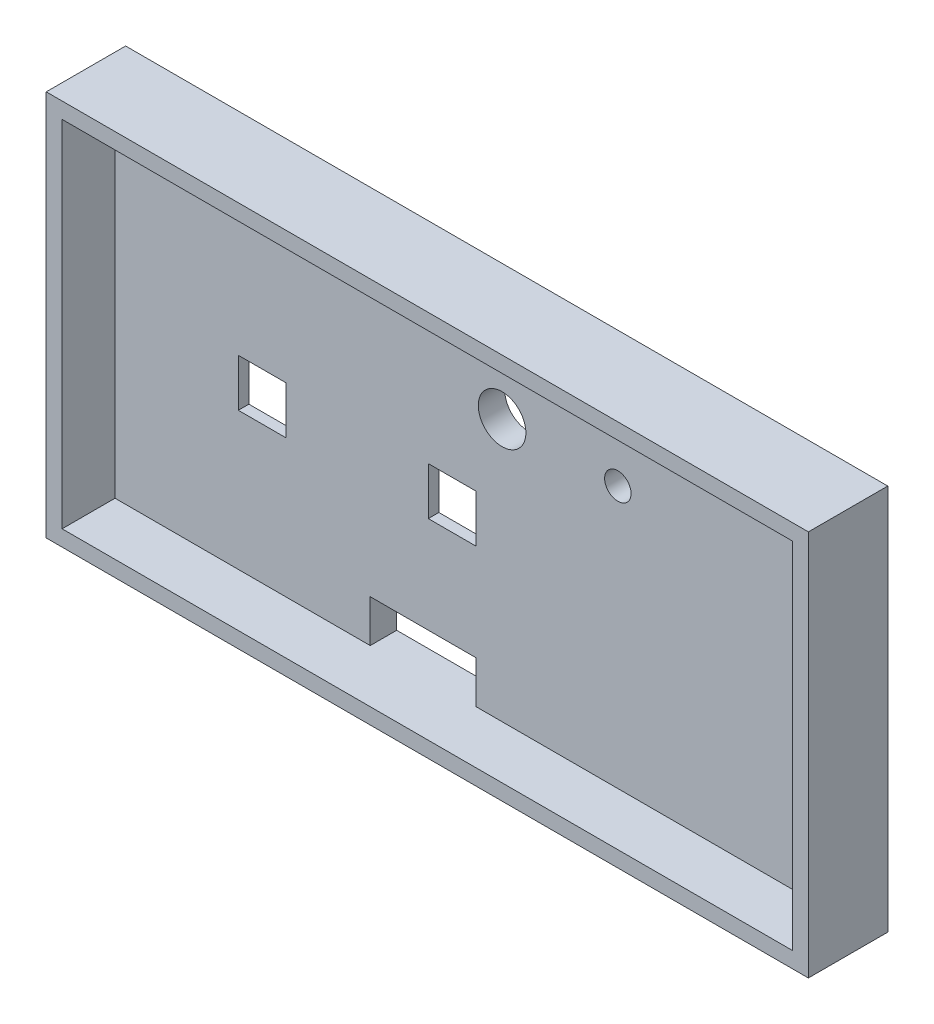
SolidWorks part; units mm, degrees
ref_plane "Plan de face" through (0, 0, 0) normal (0, 0, 1) x (1, 0, 0)
ref_plane "Plan de dessus" through (0, 0, 0) normal (0, 1, 0) x (1, 0, 0)
ref_plane "Plan de droite" through (0, 0, 0) normal (1, 0, 0) x (0, 0, -1)
sketch "Esquisse1" plane through (0, 0, 0) normal (0, 0, 1) x (1, 0, 0)
  line L1 (0, 0) -> (137, 0)
  line L2 (0, 0) -> (0, 66)
  line L3 (0, 66) -> (137, 66)
  line L4 (137, 0) -> (137, 66)
  dimension "D1" = 137
  dimension "D2" = 66
extrude "Boss.-Extru.2" add sketch "Esquisse1" along normal blind 15
sketch "Esquisse3" plane through (0, 0, 15) normal (0, 0, 1) x (1, 0, 0)
  line L0 (137, 66) -> (0, 66) construction
  line L1 (3, 3) -> (134, 3)
  line L2 (3, 3) -> (3, 63)
  line L3 (3, 63) -> (134, 63)
  line L4 (134, 3) -> (134, 63)
  line L5 (0, 0) -> (137, 0) construction
  line L6 (0, 66) -> (0, 0) construction
  line L7 (137, 0) -> (137, 66) construction
  dimension "D1" = 3
  dimension "D2" = 3
  dimension "D3" = 3
  dimension "D4" = 3
extrude "Enlèv. mat.-Extru.1" cut sketch "Esquisse3" against normal blind 10
sketch "Esquisse5" plane through (0, 0, 0) normal (0, 0, -1) x (-1, 0, 0)
  line L1 (-8.8878, 58.5065) -> (-20.8878, 58.5065)
  line L2 (-8.8878, 58.5065) -> (-8.8878, 46.5065)
  line L3 (-8.8878, 46.5065) -> (-20.8878, 46.5065)
  line L4 (-20.8878, 58.5065) -> (-20.8878, 46.5065)
  dimension "D1" = 12
  dimension "D2" = 12
extrude "Enlèv. mat.-Extru.2" cut sketch "Esquisse5" against normal blind 10 contours L2 L1 L4 L3
sketch "Esquisse6" plane through (0, 0, 0) normal (0, 0, -1) x (-1, 0, 0)
  line L1 (-36.7585, 46.5065) -> (-48.7585, 46.5065)
  line L2 (-36.7585, 46.5065) -> (-36.7585, 58.5065)
  line L3 (-36.7585, 58.5065) -> (-48.7585, 58.5065)
  line L4 (-48.7585, 46.5065) -> (-48.7585, 58.5065)
  dimension "D1" = 12
  dimension "D2" = 12
extrude "Enlèv. mat.-Extru.3" cut sketch "Esquisse6" against normal blind 10
sketch "Esquisse7" plane through (0, 0, 0) normal (0, 0, -1) x (-1, 0, 0)
  line L0 (-62.8319, 0) -> (-62.8319, 3) construction
  line L1 (0, 0) -> (-137, 0) construction
  line L3 (-62.8319, 3) -> (-47.8319, 3)
  line L4 (-62.8319, 3) -> (-62.8319, 6)
  line L5 (-62.8319, 6) -> (-47.8319, 6)
  line L6 (-47.8319, 3) -> (-47.8319, 6)
  dimension "D1" = 3
  dimension "D2" = 15
  dimension "D3" = 3
extrude "Enlèv. mat.-Extru.4" cut sketch "Esquisse7" against normal blind 10
sketch "Esquisse8" plane through (0, 0, 0) normal (0, 0, -1) x (-1, 0, 0)
  line L0 (-36.7585, 52.5065) -> (-20.8878, 52.5065) construction
  line L1 (-36.7585, 46.5065) -> (-36.7585, 58.5065) construction
  line L2 (-20.8878, 58.5065) -> (-20.8878, 46.5065) construction
  line L3 (-48.7585, 52.5065) -> (-64.6285, 52.5065) construction
  line L4 (-48.7585, 58.5065) -> (-48.7585, 46.5065) construction
  circle A0 centre (-69.1285, 52.5065) radius 4.5
  dimension "D1" = 15.8707
  dimension "D2" = 15.87
  dimension "D3" = 4.5
extrude "Enlèv. mat.-Extru.5" cut sketch "Esquisse8" against normal blind 10
sketch "Esquisse10" plane through (0, 0, 5) normal (0, 0, 1) x (1, 0, 0)
  line L0 (8.8878, 58.5065) -> (8.8878, 46.5065) construction
  line L1 (8.8878, 56.5065) -> (5.8878, 56.5065)
  line L2 (8.8878, 56.5065) -> (8.8878, 48.5065)
  line L3 (8.8878, 48.5065) -> (5.8878, 48.5065)
  line L4 (5.8878, 56.5065) -> (5.8878, 48.5065)
  dimension "D1" = 2
  dimension "D2" = 2
  dimension "D3" = 3
extrude "Boss.-Extru.3" add sketch "Esquisse10" along normal blind 4
sketch "Esquisse12" plane through (8.8878, 0, 0) normal (1, 0, 0) x (0, 0, -1)
  line L0 (-9, 56.5065) -> (-5, 56.5065) construction
  line L1 (-8, 55.5065) -> (-6, 55.5065)
  line L2 (-8, 55.5065) -> (-8, 49.5065)
  line L3 (-8, 49.5065) -> (-6, 49.5065)
  line L4 (-6, 55.5065) -> (-6, 49.5065)
  line L5 (-9, 48.5065) -> (-5, 48.5065) construction
  line L6 (-9, 48.5065) -> (-9, 56.5065) construction
  dimension "D1" = 2
  dimension "D2" = 1
  dimension "D3" = 1
  dimension "D4" = 1
extrude "Enlèv. mat.-Extru.6" cut sketch "Esquisse12" against normal blind 4
sketch "Esquisse13" plane through (0, 0, 5) normal (0, 0, 1) x (1, 0, 0)
  line L0 (20.8878, 58.5065) -> (20.8878, 46.5065) construction
  line L1 (20.8878, 56.5065) -> (23.8878, 56.5065)
  line L2 (20.8878, 56.5065) -> (20.8878, 48.5065)
  line L3 (20.8878, 48.5065) -> (23.8878, 48.5065)
  line L4 (23.8878, 56.5065) -> (23.8878, 48.5065)
  dimension "D1" = 2
  dimension "D2" = 8
  dimension "D3" = 3
extrude "Boss.-Extru.4" add sketch "Esquisse13" along normal blind 4
sketch "Esquisse14" plane through (23.8878, 0, 0) normal (1, 0, 0) x (0, 0, -1)
  line L0 (-9, 48.5065) -> (-9, 56.5065) construction
  line L1 (-8, 55.5065) -> (-6, 55.5065)
  line L2 (-8, 55.5065) -> (-8, 49.5065)
  line L3 (-8, 49.5065) -> (-6, 49.5065)
  line L4 (-6, 55.5065) -> (-6, 49.5065)
  line L5 (-9, 48.5065) -> (-5, 48.5065) construction
  dimension "D1" = 1
  dimension "D2" = 6
  dimension "D3" = 1
  dimension "D4" = 2
extrude "Enlèv. mat.-Extru.7" cut sketch "Esquisse14" against normal blind 4
sketch "Esquisse16" plane through (0, 0, 5) normal (0, 0, 1) x (1, 0, 0)
  line L0 (36.7585, 46.5065) -> (36.7585, 58.5065) construction
  line L1 (36.7585, 56.5065) -> (33.7585, 56.5065)
  line L2 (36.7585, 56.5065) -> (36.7585, 48.5065)
  line L3 (36.7585, 48.5065) -> (33.7585, 48.5065)
  line L4 (33.7585, 56.5065) -> (33.7585, 48.5065)
  dimension "D1" = 2
  dimension "D2" = 2
  dimension "D3" = 3
extrude "Boss.-Extru.5" add sketch "Esquisse16" along normal blind 4
sketch "Esquisse17" plane through (0, 0, 5) normal (0, 0, 1) x (1, 0, 0)
  line L0 (48.7585, 58.5065) -> (48.7585, 46.5065) construction
  line L1 (48.7585, 56.5065) -> (51.7585, 56.5065)
  line L2 (48.7585, 56.5065) -> (48.7585, 48.5065)
  line L3 (48.7585, 48.5065) -> (51.7585, 48.5065)
  line L4 (51.7585, 56.5065) -> (51.7585, 48.5065)
  line L5 (36.7585, 48.5065) -> (36.7585, 56.5065) construction
  dimension "D1" = 3
  dimension "D2" = 2
  dimension "D3" = 2
extrude "Boss.-Extru.6" add sketch "Esquisse17" along normal up to vertex (4 mm away)
ref_plane "Plan1" through (8.8878, 48.5065, 9) normal (0, 1, 0) x (1, 0, 0)
sketch "Esquisse19" plane through (36.7585, 0, 0) normal (1, 0, 0) x (0, 0, -1)
  line L0 (-9, 56.5065) -> (-5, 56.5065) construction
  line L1 (-8, 55.5065) -> (-6, 55.5065)
  line L2 (-8, 55.5065) -> (-8, 49.5065)
  line L3 (-8, 49.5065) -> (-6, 49.5065)
  line L4 (-6, 55.5065) -> (-6, 49.5065)
  line L5 (-9, 48.5065) -> (-5, 48.5065) construction
  line L6 (-9, 48.5065) -> (-9, 56.5065) construction
  dimension "D1" = 1
  dimension "D2" = 1
  dimension "D3" = 1
  dimension "D4" = 6
  dimension "D5" = 2
extrude "Enlèv. mat.-Extru.9" cut sketch "Esquisse19" against normal blind 3
sketch "Esquisse20" plane through (51.7585, 0, 0) normal (1, 0, 0) x (0, 0, -1)
  line L0 (-9, 56.5065) -> (-5, 56.5065) construction
  line L1 (-8, 55.5065) -> (-6, 55.5065)
  line L2 (-8, 55.5065) -> (-8, 49.5065)
  line L3 (-8, 49.5065) -> (-6, 49.5065)
  line L4 (-6, 55.5065) -> (-6, 49.5065)
  line L5 (-9, 48.5065) -> (-5, 48.5065) construction
  line L7 (-9, 48.5065) -> (-9, 56.5065) construction
  dimension "D1" = 1
  dimension "D2" = 1
  dimension "D3" = 1
  dimension "D4" = 2
extrude "Enlèv. mat.-Extru.10" cut sketch "Esquisse20" against normal blind 3
sketch "Esquisse21" plane through (0, 0, 0) normal (0, 0, -1) x (-1, 0, 0)
  line L0 (-73.6285, 52.5065) -> (-89.4985, 52.5065) construction
  circle A0 centre (-69.1285, 52.5065) radius 4.5 construction
  circle A1 centre (-90.9985, 52.5065) radius 1.5
  dimension "D2" = 3
  dimension "D1" = 15.87
extrude "Enlèv. mat.-Extru.12" cut sketch "Esquisse21" against normal blind 21
sketch "Esquisse22" plane through (0, 0, 9) normal (0, 0, 1) x (1, 0, 0)
  line L1 (48.7585, 56.5065) -> (51.7585, 56.5065)
  line L2 (48.7585, 56.5065) -> (48.7585, 48.5065)
  line L3 (48.7585, 48.5065) -> (51.7585, 48.5065)
  line L4 (51.7585, 56.5065) -> (51.7585, 48.5065)
extrude "Enlèv. mat.-Extru.13" cut sketch "Esquisse22" against normal blind 4
sketch "Esquisse23" plane through (0, 0, 9) normal (0, 0, 1) x (1, 0, 0)
  line L1 (33.7585, 56.5065) -> (36.7585, 56.5065)
  line L2 (33.7585, 56.5065) -> (33.7585, 48.5065)
  line L3 (33.7585, 48.5065) -> (36.7585, 48.5065)
  line L4 (36.7585, 56.5065) -> (36.7585, 48.5065)
extrude "Enlèv. mat.-Extru.14" cut sketch "Esquisse23" against normal blind 4
sketch "Esquisse24" plane through (0, 0, 9) normal (0, 0, 1) x (1, 0, 0)
  line L1 (20.8878, 56.5065) -> (23.8878, 56.5065)
  line L2 (20.8878, 56.5065) -> (20.8878, 48.5065)
  line L3 (20.8878, 48.5065) -> (23.8878, 48.5065)
  line L4 (23.8878, 56.5065) -> (23.8878, 48.5065)
extrude "Enlèv. mat.-Extru.15" cut sketch "Esquisse24" against normal blind 4
sketch "Esquisse25" plane through (0, 0, 9) normal (0, 0, 1) x (1, 0, 0)
  line L2 (8.8878, 48.5065) -> (5.8878, 48.5065)
  line L3 (8.8878, 48.5065) -> (8.8878, 56.5065)
  line L4 (8.8878, 56.5065) -> (5.8878, 56.5065)
  line L5 (5.8878, 48.5065) -> (5.8878, 56.5065)
extrude "Enlèv. mat.-Extru.16" cut sketch "Esquisse25" against normal blind 4
sketch "Esquisse28" plane through (0, 0, 0) normal (0, 0, -1) x (-1, 0, 0)
  line L1 (-20.8878, 58.5065) -> (-8.8878, 58.5065)
  line L2 (-20.8878, 58.5065) -> (-20.8878, 46.5065)
  line L3 (-20.8878, 46.5065) -> (-8.8878, 46.5065)
  line L4 (-8.8878, 58.5065) -> (-8.8878, 46.5065)
extrude "Boss.-Extru.7" add sketch "Esquisse28" against normal blind 5
sketch "Esquisse30" plane through (0, 0, 5) normal (0, 0, 1) x (1, 0, 0)
  line L0 (36.7585, 46.5065) -> (28.2934, 38.0414) construction
  line L2 (28.2934, 38.0414) -> (19.2934, 38.0414)
  line L3 (28.2934, 38.0414) -> (28.2934, 29.0414)
  line L4 (28.2934, 29.0414) -> (19.2934, 29.0414)
  line L5 (19.2934, 38.0414) -> (19.2934, 29.0414)
  dimension "D1" = 9
  dimension "D2" = 9
extrude "Enlèv. mat.-Extru.17" cut sketch "Esquisse30" against normal blind 2.5
sketch "Esquisse32" plane through (0, 0, 5) normal (0, 0, 1) x (1, 0, 0)
  line L1 (28.2934, 38.0414) -> (19.2934, 38.0414)
  line L2 (28.2934, 38.0414) -> (28.2934, 29.0414)
  line L3 (28.2934, 29.0414) -> (19.2934, 29.0414)
  line L4 (19.2934, 38.0414) -> (19.2934, 29.0414)
extrude "Enlèv. mat.-Extru.18" cut sketch "Esquisse32" against normal blind 8.5
sketch "Esquisse33" plane through (0, 0, 0) normal (0, 0, -1) x (-1, 0, 0)
  line L0 (-28.2934, 38.0414) -> (-19.2934, 29.0414) construction
  line L1 (-19.2934, 29.0414) -> (-8.9572, 18.7052) construction
  line L2 (-8.9572, 18.7052) -> (-35.8241, 45.5721) construction
  line L3 (-28.2934, 29.0414) -> (-19.2934, 38.0414) construction
  line L4 (-19.2934, 38.0414) -> (-9.807, 47.5277) construction
  line L5 (-9.807, 47.5277) -> (-37.0078, 20.327) construction
  line L7 (-31.7648, 41.5128) -> (-15.7648, 41.5128)
  line L8 (-31.7648, 41.5128) -> (-31.7648, 25.5128)
  line L9 (-31.7648, 25.5128) -> (-15.7648, 25.5128)
  line L10 (-15.7648, 41.5128) -> (-15.7648, 25.5128)
  dimension "D1" = 16
  dimension "D2" = 16
extrude "Enlèv. mat.-Extru.19" cut sketch "Esquisse33" against normal blind 3
sketch "Esquisse34" plane through (0, 0, 0) normal (0, 0, -1) x (-1, 0, 0)
  line L0 (-31.7648, 41.5128) -> (-51.4375, 41.5128) construction
  line L2 (-51.4375, 41.5128) -> (-67.4375, 41.5128)
  line L3 (-51.4375, 41.5128) -> (-51.4375, 25.5128)
  line L4 (-51.4375, 25.5128) -> (-67.4375, 25.5128)
  line L5 (-67.4375, 41.5128) -> (-67.4375, 25.5128)
  dimension "D1" = 16
  dimension "D2" = 16
extrude "Enlèv. mat.-Extru.20" cut sketch "Esquisse34" against normal blind 3
sketch "Esquisse35" plane through (0, 0, 3) normal (0, 0, -1) x (-1, 0, 0)
  line L0 (-67.4375, 41.5128) -> (-51.4375, 25.5128) construction
  line L1 (-51.4375, 41.5128) -> (-67.4375, 25.5128) construction
  line L3 (-64.1884, 38.2637) -> (-55.1884, 38.2637)
  line L4 (-64.1884, 38.2637) -> (-64.1884, 29.2637)
  line L5 (-64.1884, 29.2637) -> (-55.1884, 29.2637)
  line L6 (-55.1884, 38.2637) -> (-55.1884, 29.2637)
  dimension "D1" = 9
  dimension "D2" = 9
extrude "Enlèv. mat.-Extru.21" cut sketch "Esquisse35" against normal blind 3
sketch "Esquisse36" plane through (0, 0, 0) normal (0, 0, -1) x (-1, 0, 0)
  line L1 (-48.7585, 58.5065) -> (-36.7585, 58.5065)
  line L2 (-48.7585, 58.5065) -> (-48.7585, 46.5065)
  line L3 (-48.7585, 46.5065) -> (-36.7585, 46.5065)
  line L4 (-36.7585, 58.5065) -> (-36.7585, 46.5065)
extrude "Boss.-Extru.8" add sketch "Esquisse36" against normal blind 5
sketch "Esquisse37" plane through (0, 0, 0) normal (0, 0, -1) x (-1, 0, 0)
  line L0 (-92.4985, 52.5065) -> (-89.4985, 52.5065) construction
  line L1 (-90.9985, 54.0065) -> (-90.9985, 51.0065) construction
  circle A0 centre (-90.9985, 52.5065) radius 1.5 construction
  circle A1 centre (-90.9985, 52.5065) radius 2.5
  dimension "D1" = 5
extrude "Enlèv. mat.-Extru.22" cut sketch "Esquisse37" against normal blind 5
sketch "Esquisse39" plane through (0, 0, 15) normal (0, 0, 1) x (1, 0, 0)
  line L0 (0, 66) -> (0, 0) construction
  line L1 (3, 63) -> (0, 63)
  line L2 (3, 63) -> (3, 3)
  line L3 (3, 3) -> (0, 3)
  line L4 (0, 63) -> (0, 3)
extrude "Enlèv. mat.-Extru.23" cut sketch "Esquisse39" against normal blind 10
sketch "Esquisse40" plane through (0, 0, 0) normal (-1, 0, 0) x (0, 0, 1)
  line L0 (15, 0) -> (0, 0) construction
  line L1 (0, 66) -> (5, 66)
  line L2 (0, 66) -> (0, 0)
  line L3 (0, 0) -> (5, 0)
  line L4 (5, 66) -> (5, 0)
extrude "Boss.-Extru.9" add sketch "Esquisse40" along normal blind 7
sketch "Esquisse41" plane through (0, 0, 5) normal (0, 0, 1) x (1, 0, 0)
  line L0 (-7, 0) -> (0, 0) construction
  line L1 (-7, 66) -> (-4, 66)
  line L2 (-7, 66) -> (-7, 0)
  line L3 (-7, 0) -> (-4, 0)
  line L4 (-4, 66) -> (-4, 0)
  dimension "D1" = 3
extrude "Boss.-Extru.10" add sketch "Esquisse41" along normal blind 10
sketch "Esquisse42" plane through (0, 0, 5) normal (0, 0, 1) x (1, 0, 0)
  line L1 (0, 3) -> (-4, 3)
  line L2 (0, 3) -> (0, 0)
  line L3 (0, 0) -> (-4, 0)
  line L4 (-4, 3) -> (-4, 0)
extrude "Boss.-Extru.11" add sketch "Esquisse42" along normal blind 10
sketch "Esquisse43" plane through (0, 0, 5) normal (0, 0, 1) x (1, 0, 0)
  line L0 (-4, 3) -> (-4, 66) construction
  line L1 (0, 66) -> (-4, 66)
  line L2 (0, 66) -> (0, 63)
  line L3 (0, 63) -> (-4, 63)
  line L4 (-4, 66) -> (-4, 63)
extrude "Boss.-Extru.12" add sketch "Esquisse43" along normal blind 10
sketch "Esquisse44" plane through (0, 0, 5) normal (0, 0, 1) x (1, 0, 0)
  line L2 (62.8319, 3) -> (134, 3) construction
  line L3 (64.2169, 3) -> (44.2169, 3)
  line L4 (64.2169, 3) -> (64.2169, 11)
  line L5 (64.2169, 11) -> (44.2169, 11)
  line L6 (44.2169, 3) -> (44.2169, 11)
  dimension "D1" = 8
  dimension "D2" = 20
extrude "Enlèv. mat.-Extru.24" cut sketch "Esquisse44" against normal blind 10
ref_plane "Plan2" through (-4, 3, 15) normal (0, 1, 0) x (1, 0, 0)
sketch "Esquisse46" plane through (0, 0, 5) normal (0, 0, 1) x (1, 0, 0)
  line L1 (137, 66) -> (-7, 66) construction
  line L2 (-4, 63) -> (134, 63)
  line L3 (-4, 63) -> (-4, 66)
  line L4 (-4, 66) -> (134, 66)
  line L5 (134, 63) -> (134, 66)
extrude "Enlèv. mat.-Extru.25" cut sketch "Esquisse46" along normal blind 10
sketch "Esquisse47" plane through (0, 66, 0) normal (0, 1, 0) x (1, 0, 0)
  line L1 (-7, 0) -> (134, 0)
  line L2 (-7, 0) -> (-7, -5)
  line L3 (-7, -5) -> (134, -5)
  line L4 (134, 0) -> (134, -5)
extrude "Boss.-Extru.13" add sketch "Esquisse47" along normal blind 7
sketch "Esquisse48" plane through (0, 0, 5) normal (0, 0, 1) x (1, 0, 0)
  line L0 (134, 73) -> (134, 66) construction
  line L1 (-7, 73) -> (134, 73)
  line L2 (-7, 73) -> (-7, 69.9954)
  line L3 (-7, 69.9954) -> (134, 69.9954)
  line L4 (134, 73) -> (134, 69.9954)
extrude "Boss.-Extru.14" add sketch "Esquisse48" along normal blind 10
sketch "Esquisse49" plane through (0, 0, 5) normal (0, 0, 1) x (1, 0, 0)
  line L1 (-7, 69.9954) -> (-4, 69.9954)
  line L2 (-7, 69.9954) -> (-7, 66)
  line L3 (-7, 66) -> (-4, 66)
  line L4 (-4, 69.9954) -> (-4, 66)
extrude "Boss.-Extru.15" add sketch "Esquisse49" along normal blind 10
sketch "Esquisse50" plane through (0, 66, 0) normal (0, 1, 0) x (1, 0, 0)
  line L1 (134, 0) -> (137, 0)
  line L2 (134, 0) -> (134, -15)
  line L3 (134, -15) -> (137, -15)
  line L4 (137, 0) -> (137, -15)
extrude "Boss.-Extru.16" add sketch "Esquisse50" along normal blind 7
